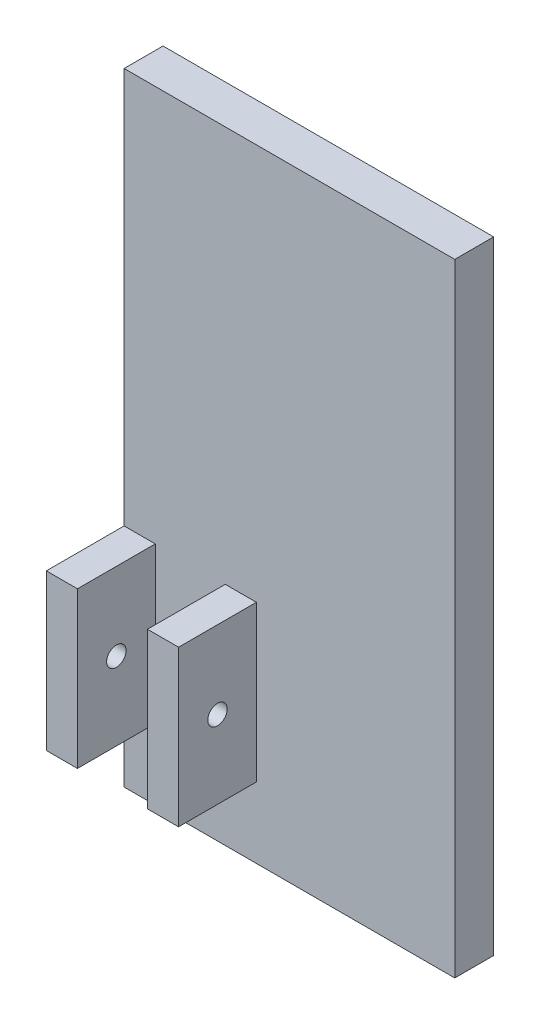
SolidWorks part; units mm, degrees
ref_plane "Plan de face" through (0, 0, 0) normal (0, 0, 1) x (1, 0, 0)
ref_plane "Plan de dessus" through (0, 0, 0) normal (0, 1, 0) x (1, 0, 0)
ref_plane "Plan de droite" through (0, 0, 0) normal (1, 0, 0) x (0, 0, -1)
sketch "Sketch1" plane through (0, 0, 0) normal (0, 0, 1) x (1, 0, 0)
  line L2 (-15, -4) -> (-15, 156)
  line L3 (-15, 156) -> (70, 156)
  line L4 (70, -4) -> (70, 156)
  line L5 (70, -4) -> (-15, -4)
  dimension "D1" = 4
  dimension "D2" = 85
  dimension "D3" = 160
  dimension "D4" = 15
extrude "Boss-Extrude1" add sketch "Sketch1" along normal blind 10
sketch "Sketch2" plane through (0, 0, 10) normal (0, 0, 1) x (1, 0, 0)
  line L0 (-15, 156) -> (-15, -4) construction
  line L1 (-15, 14.15) -> (-7, 14.15)
  line L2 (-15, 14.15) -> (-15, 54.15)
  line L3 (-15, 54.15) -> (-7, 54.15)
  line L4 (-7, 14.15) -> (-7, 54.15)
  line L5 (-15, -4) -> (70, -4) construction
  line L6 (-15, 34.15) -> (-7, 34.15) construction
  dimension "D1" = 20
  dimension "D2" = 38.15
  dimension "D3" = 8
extrude "Boss-Extrude2" add sketch "Sketch2" along normal blind 20
sketch "Sketch4" plane through (0, 0, 10) normal (0, 0, 1) x (1, 0, 0)
  line L0 (-7, 54.15) -> (-15, 54.15) construction
  line L1 (11, 54.15) -> (19, 54.15)
  line L2 (11, 54.15) -> (11, 14.15)
  line L3 (11, 14.15) -> (19, 14.15)
  line L4 (19, 54.15) -> (19, 14.15)
  line L5 (-15, 14.15) -> (-7, 14.15) construction
  dimension "D1" = 8
  dimension "D2" = 18
extrude "Boss-Extrude3" add sketch "Sketch4" along normal up to surface (590.1297 mm away)
sketch "Sketch3" plane through (-15, 0, 0) normal (-1, 0, 0) x (0, 0, 1)
  line L0 (30, 54.15) -> (10, 54.15) construction
  line L1 (30, 54.15) -> (30, 14.15) construction
  circle A0 centre (20, 34.15) radius 2.5
  dimension "D1" = 5
  dimension "D2" = 20
  dimension "D3" = 10
extrude "Cut-Extrude1" cut sketch "Sketch3" against normal up to surface (34 mm away) up to face at (19, 34.15, 20)
